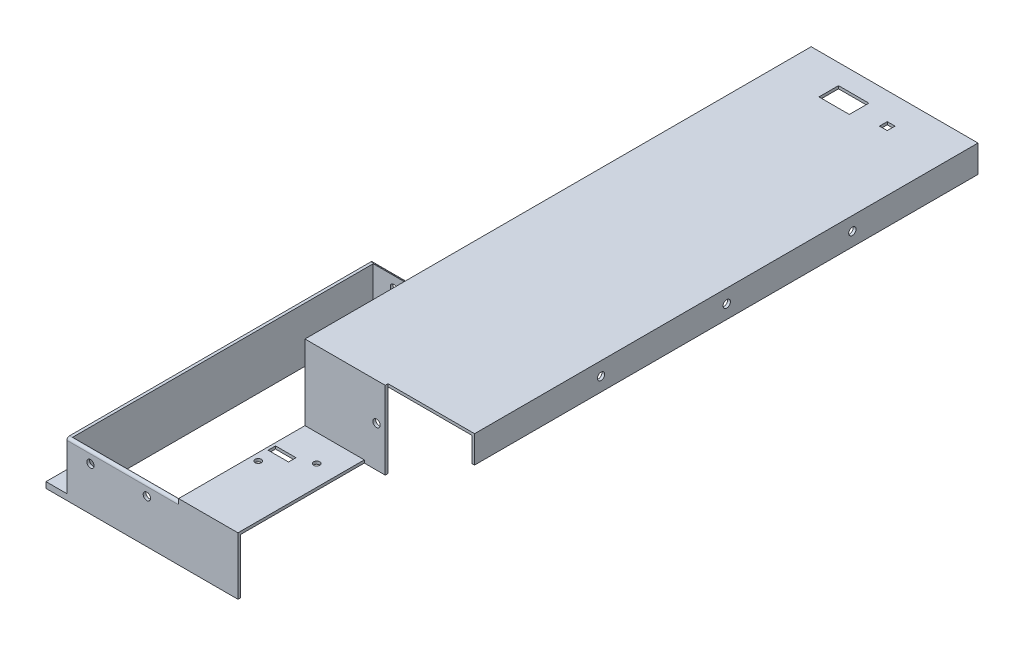
SolidWorks part; units mm, degrees
material "ABS PC"
ref_plane "Front Plane" through (0, 0, 0) normal (0, 0, 1) x (1, 0, 0)
ref_plane "Top Plane" through (0, 0, 0) normal (0, 1, 0) x (1, 0, 0)
ref_plane "Right Plane" through (0, 0, 0) normal (1, 0, 0) x (0, 0, -1)
sketch "Sketch1" plane through (0, 0, 0) normal (0, 1, 0) x (1, 0, 0)
  line L0 (0, 0) -> (0, 187.5)
  line L1 (0, 187.5) -> (64, 187.5)
  line L2 (64, 187.5) -> (64, 374.5)
  line L3 (0, 0) -> (1.6, 0)
  line L4 (1.6, 0) -> (1.6, 153.4)
  line L5 (1.6, 153.4) -> (65.6, 153.4)
  line L6 (65.6, 153.4) -> (65.6, 374.5)
  line L7 (65.6, 374.5) -> (64, 374.5)
  dimension "D4" = 1.6
  dimension "D1" = 187.5
  dimension "D2" = 64
  dimension "D3" = 187
  dimension "D5" = 153.4
  dimension "D6" = 1.6
extrude "Boss-Extrude1" add sketch "Sketch1" along normal blind 76
sketch "Sketch2" plane through (0, 0, 0) normal (-1, 0, 0) x (0, 0, 1)
  line L0 (0, 76) -> (-187.5, 76)
  line L1 (-187.5, 76) -> (-187.5, 33.4)
  line L2 (-187.5, 76) -> (-187.5, 0) construction
  line L3 (-187.5, 33.4) -> (0, 33.4)
  line L4 (0, 76) -> (0, 0) construction
  line L5 (0, 33.4) -> (0, 76)
  dimension "D1" = 42.6
extrude "Cut-Extrude1" cut sketch "Sketch2" against normal up to surface (64 mm away) up to face at (64, 38, -281)
sketch "Sketch3" plane through (0, 0, 0) normal (0, -1, 0) x (1, 0, 0)
  line L0 (0, 0) -> (-12, 0)
  line L1 (-12, 0) -> (-12, -199.5)
  line L2 (-12, -199.5) -> (52, -199.5)
  line L3 (52, -199.5) -> (52, -374.5)
  line L4 (0, 0) -> (0, -187.5)
  line L5 (0, -187.5) -> (64, -187.5)
  line L6 (64, -187.5) -> (64, -374.5)
  line L7 (52, -374.5) -> (64, -374.5)
  dimension "D1" = 12
  dimension "D2" = 12
  dimension "D3" = 12
extrude "Boss-Extrude2" add sketch "Sketch3" against normal blind 3.4
sketch "Sketch4" plane through (0, 0, 0) normal (0, 0, 1) x (1, 0, 0)
  line L0 (-12, 0) -> (-12, 3.4)
  line L1 (-12, 3.4) -> (0, 3.4)
  line L2 (0, 3.4) -> (-12, 3.4) construction
  line L3 (0, 33.4) -> (0, 3.4) construction
  line L4 (0, 3.4) -> (0, 33.4)
  line L5 (0, 33.4) -> (1.6, 33.4)
  line L6 (1.6, 33.4) -> (1.6, 0)
  line L7 (1.6, 0) -> (-12, 0)
extrude "Cut-Extrude2" cut sketch "Sketch4" against normal blind 12
sketch "Sketch5" plane through (0, 0, -153.4) normal (0, 0, 1) x (1, 0, 0)
  line L0 (64, 76) -> (64, 33.4)
  line L1 (64, 33.4) -> (65.6, 33.4)
  line L2 (65.6, 76) -> (65.6, 0) construction
  line L3 (65.6, 33.4) -> (65.6, 76)
  line L4 (65.6, 76) -> (64, 76)
  dimension "D1" = 42.6
extrude "Boss-Extrude3" add sketch "Sketch5" along normal up to surface (141.4 mm away) up to face at (-3.4667, 12.2667, -12)
sketch "Sketch6" plane through (1.6, 0, 0) normal (1, 0, 0) x (0, 0, -1)
  line L0 (12, 0) -> (12, 33.4)
  line L1 (12, 33.4) -> (13.6, 33.4)
  line L2 (12, 33.4) -> (153.4, 33.4) construction
  line L3 (13.6, 33.4) -> (13.6, 0)
  line L4 (12, 0) -> (153.4, 0) construction
  line L5 (13.6, 0) -> (12, 0)
  dimension "D1" = 1.6
extrude "Boss-Extrude4" add sketch "Sketch6" along normal blind 158
sketch "Sketch7" plane through (65.6, 0, 0) normal (1, 0, 0) x (0, 0, -1)
  line L0 (12, 33.4) -> (12, 35)
  line L1 (12, 76) -> (12, 33.4) construction
  line L2 (12, 33.4) -> (86, 33.4)
  line L3 (153.4, 33.4) -> (13.6, 33.4) construction
  line L4 (12, 35) -> (86, 35)
  line L5 (86, 35) -> (86, 33.4)
  dimension "D1" = 1.6
  dimension "D2" = 74
extrude "Boss-Extrude5" add sketch "Sketch7" along normal blind 94
sketch "Sketch8" plane through (0, 0, -12) normal (0, 0, 1) x (1, 0, 0)
  line L0 (65.6, 35) -> (64, 35)
  line L1 (64, 33.4) -> (64, 76) construction
  line L2 (64, 35) -> (64, 76)
  line L3 (64, 76) -> (65.6, 76)
  line L4 (65.6, 76) -> (65.6, 35)
extrude "Cut-Extrude3" cut sketch "Sketch8" against normal up to surface (74 mm away) up to face at (112.6, 34.2, -86)
sketch "Sketch10" plane through (0, 0, -86) normal (0, 0, 1) x (1, 0, 0)
  line L0 (64, 35) -> (159.6, 35)
  line L1 (64, 35) -> (64, 76)
  line L2 (64, 76) -> (159.6, 76)
  line L3 (159.6, 76) -> (159.6, 35)
extrude "Boss-Extrude8" add sketch "Sketch10" along normal blind 1.6
sketch "Sketch11" plane through (0, 33.4, 0) normal (0, 1, 0) x (1, 0, 0)
  line L0 (1.6, 153.4) -> (1.6, 185.9)
  line L1 (1.6, 185.9) -> (64, 185.9)
  line L2 (64, 187.5) -> (64, 153.4) construction
  line L3 (64, 185.9) -> (64, 153.4)
  line L4 (64, 153.4) -> (1.6, 153.4)
  dimension "D1" = 32.5
extrude "Cut-Extrude4" cut sketch "Sketch11" against normal up to surface (33.4 mm away) up to face at (53.36, 0, -150.6)
sketch "Sketch12" plane through (0, 0, 0) normal (0, -1, 0) x (1, 0, 0)
  line L0 (64, -153.4) -> (65.6, -153.4)
  line L1 (64, -153.4) -> (64, -185.9)
  line L2 (64, -185.9) -> (65.6, -185.9)
  line L3 (65.6, -153.4) -> (65.6, -374.5) construction
  line L4 (65.6, -185.9) -> (65.6, -153.4)
extrude "Cut-Extrude5" cut sketch "Sketch12" against normal up to surface (33.4 mm away) up to face at (96.4, 33.4, -84.3333)
sketch "Sketch13" plane through (0, 0, -12) normal (0, 0, 1) x (1, 0, 0)
  line L0 (159.6, 0) -> (159.6, 76)
  line L1 (159.6, 76) -> (98, 76)
  line L2 (159.6, 76) -> (64, 76) construction
  line L3 (98, 76) -> (98, 0)
  line L4 (-12, 0) -> (159.6, 0) construction
  line L5 (98, 0) -> (159.6, 0)
  dimension "D1" = 61.6
extrude "Cut-Extrude6" cut sketch "Sketch13" against normal up to surface (74 mm away) up to face at (112.6, 54.7, -86)
sketch "Sketch16" plane through (98, 0, 0) normal (1, 0, 0) x (0, 0, -1)
  line L0 (86, 76) -> (84.4, 76)
  line L1 (84.4, 76) -> (84.4, 33.4)
  line L2 (86, 33.4) -> (13.6, 33.4) construction
  line L3 (84.4, 33.4) -> (86, 33.4)
  line L4 (86, 33.4) -> (86, 76)
extrude "Boss-Extrude11" add sketch "Sketch16" along normal blind 12
sketch "Sketch17" plane through (65.6, 0, 0) normal (1, 0, 0) x (0, 0, -1)
  line L0 (86, 76) -> (374.5, 76)
  line L1 (374.5, 74.4) -> (86, 74.4)
  line L2 (86, 33.4) -> (86, 76) construction
  line L3 (86, 74.4) -> (86, 76)
  line L4 (374.5, 74.4) -> (374.5, 76)
  dimension "D1" = 1.6
extrude "Boss-Extrude12" add sketch "Sketch17" along normal blind 94 contours L4 L0 L3 L1
sketch "Sketch18" plane through (0, 74.4, 0) normal (0, -1, 0) x (1, 0, 0)
  line L0 (159.6, -86) -> (159.6, -374.5)
  line L1 (159.6, -374.5) -> (158, -374.5)
  line L2 (159.6, -374.5) -> (65.6, -374.5) construction
  line L3 (158, -374.5) -> (158, -86)
  line L4 (159.6, -86) -> (110, -86) construction
  line L5 (158, -86) -> (159.6, -86)
  dimension "D1" = 1.6
extrude "Boss-Extrude13" add sketch "Sketch18" along normal blind 14
sketch "Sketch19" plane through (0, 35, 0) normal (0, 1, 0) x (1, 0, 0)
  circle A0 centre (68.1713, 53.4357) radius 1.75
  circle A1 centre (86.1713, 68.9357) radius 1.76
extrude "Cut-Extrude7" cut sketch "Sketch19" against normal blind 5
sketch "Sketch20" plane through (0, 0, -187.5) normal (0, 0, -1) x (-1, 0, 0)
  circle A0 centre (-45.7912, 25) radius 2.1
  circle A1 centre (-13.4918, 25) radius 2.1
extrude "Cut-Extrude9" cut sketch "Sketch20" against normal blind 195
sketch "Sketch21" plane through (0, 3.4, 0) normal (0, 1, 0) x (1, 0, 0)
  line L0 (58, 374.5) -> (58, 316.5)
  line L1 (52, 374.5) -> (64, 374.5) construction
  line L2 (58, 316.5) -> (58, 258.5)
  line L3 (20, 199.5) -> (20, 194.5)
  line L4 (-12, 199.5) -> (52, 199.5) construction
  line L5 (-6, 12) -> (-6, 72)
  line L6 (0, 12) -> (-12, 12) construction
  line L7 (-6, 72) -> (-6, 132)
  circle A0 centre (58, 316.5) radius 2.5
  circle A1 centre (58, 258.5) radius 2.5
  circle A2 centre (20, 194.5) radius 2.5
  circle A3 centre (-6, 72) radius 2.5
  circle A4 centre (-6, 132) radius 2.5
  dimension "D3" = 5
  dimension "D4" = 60
  dimension "D6" = 5
  dimension "D7" = 5
  dimension "D8" = 5
  dimension "D9" = 5
  dimension "D10" = 5
  dimension "D1" = 58
  dimension "D2" = 58
  dimension "D5" = 60
extrude "Cut-Extrude10" cut sketch "Sketch21" against normal blind 10
sketch "Sketch22" plane through (159.6, 0, 0) normal (1, 0, 0) x (0, 0, -1)
  line L0 (374.5, 68.2) -> (302.5, 68.2)
  line L1 (374.5, 60.4) -> (374.5, 76) construction
  line L2 (302.5, 68.2) -> (230.5, 68.2)
  line L3 (230.5, 68.2) -> (158.5, 68.2)
  circle A0 centre (302.5, 68.2) radius 2.1
  circle A1 centre (230.5, 68.2) radius 2.1
  circle A2 centre (158.5, 68.2) radius 2.1
  dimension "D1" = 72
  dimension "D4" = 4.2
  dimension "D5" = 4.2
  dimension "D6" = 4.2
  dimension "D2" = 72
  dimension "D3" = 72
extrude "Cut-Extrude11" cut sketch "Sketch22" against normal blind 4
sketch "Sketch23" plane through (0, 0, -84.4) normal (0, 0, 1) x (1, 0, 0)
  line L0 (110, 54.7) -> (105, 54.7)
  line L1 (110, 76) -> (110, 33.4) construction
  circle A0 centre (105, 54.7) radius 2.1
  dimension "D2" = 4.2
  dimension "D1" = 5
extrude "Cut-Extrude12" cut sketch "Sketch23" against normal blind 4
sketch "Sketch25" plane through (0, 76, 0) normal (0, 1, 0) x (1, 0, 0)
  line L1 (91.1471, 351.8133) -> (108.5471, 351.8133)
  line L2 (91.1471, 351.8133) -> (91.1471, 363.0133)
  line L3 (91.1471, 363.0133) -> (108.5471, 363.0133)
  line L4 (108.5471, 351.8133) -> (108.5471, 363.0133)
  line L5 (122.9897, 354.6654) -> (127.4323, 354.6654)
  line L6 (122.9897, 354.6654) -> (122.9897, 359.1081)
  line L7 (122.9897, 359.1081) -> (127.4323, 359.1081)
  line L8 (127.4323, 354.6654) -> (127.4323, 359.1081)
  circle A0 centre (122.9897, 354.8654) radius 0.2 construction
extrude "Cut-Extrude13" cut sketch "Sketch25" against normal blind 4
sketch "Sketch27" plane through (0, 33.4, 0) normal (0, 1, 0) x (1, 0, 0)
  line L1 (0, 12) -> (64, 12)
  line L2 (0, 12) -> (0, 187.5)
  line L3 (0, 187.5) -> (64, 187.5)
  line L4 (64, 12) -> (64, 187.5)
extrude "Cut-Extrude15" cut sketch "Sketch27" against normal blind 2
sketch "Sketch28" plane through (64, 0, 0) normal (-1, 0, 0) x (0, 0, 1)
  line L0 (-84.4, 35) -> (-84.4, 33.4)
  line L1 (-84.4, 33.4) -> (-13.6, 33.4)
  line L2 (-13.6, 31.4) -> (-13.6, 33.4) construction
  line L3 (-13.6, 33.4) -> (-185.9, 33.4) construction
  line L4 (-13.6, 33.4) -> (-13.6, 31.4)
  line L5 (-13.6, 31.4) -> (-12, 31.4)
  line L6 (-12, 31.4) -> (-12, 35)
  line L7 (-12, 35) -> (-84.4, 35)
extrude "Cut-Extrude16" cut sketch "Sketch28" against normal blind 52
sketch "Sketch29" plane through (0, 33.4, 0) normal (0, -1, 0) x (1, 0, 0)
  line L0 (110, -86) -> (110, -84.4)
  line L1 (110, -84.4) -> (64, -84.4)
  line L2 (64, -84.4) -> (64, -185.9)
  line L3 (64, -185.9) -> (65.6, -185.9)
  line L4 (65.6, -185.9) -> (65.6, -86)
  line L5 (65.6, -86) -> (110, -86)
extrude "Boss-Extrude14" add sketch "Sketch29" along normal blind 2
sketch "Sketch33" plane through (0, 0, -12) normal (0, 0, 1) x (1, 0, 0)
  line L0 (64, 76) -> (64, 31.4) construction
  line L1 (98, 31.4) -> (64, 31.4)
  line L2 (98, 31.4) -> (98, 33)
  line L3 (98, 33) -> (64, 33)
  line L4 (64, 31.4) -> (64, 33)
  dimension "D1" = 1.6
extrude "Boss-Extrude16" add sketch "Sketch33" against normal up to surface (72.4 mm away) up to face at (87, 53.7, -84.4)
fillet "Fillet1" radius 1.5 2 edges at (32, 31.4, -187.5) (32, 31.4, -12)
sketch "Sketch34" plane through (0, 33, 0) normal (0, 1, 0) x (1, 0, 0)
  circle A0 centre (86.1713, 68.9357) radius 1.76
  circle A1 centre (68.1713, 53.4357) radius 1.75
extrude "Cut-Extrude17" cut sketch "Sketch34" against normal blind 10
sketch "Sketch35" plane through (0, 33, 0) normal (0, 1, 0) x (1, 0, 0)
  line L1 (65.6173, 61.6298) -> (77.3653, 61.6298)
  line L2 (65.6173, 61.6298) -> (65.6173, 65.9101)
  line L3 (65.6173, 65.9101) -> (77.3653, 65.9101)
  line L4 (77.3653, 61.6298) -> (77.3653, 65.9101)
extrude "Cut-Extrude18" cut sketch "Sketch35" against normal blind 10
